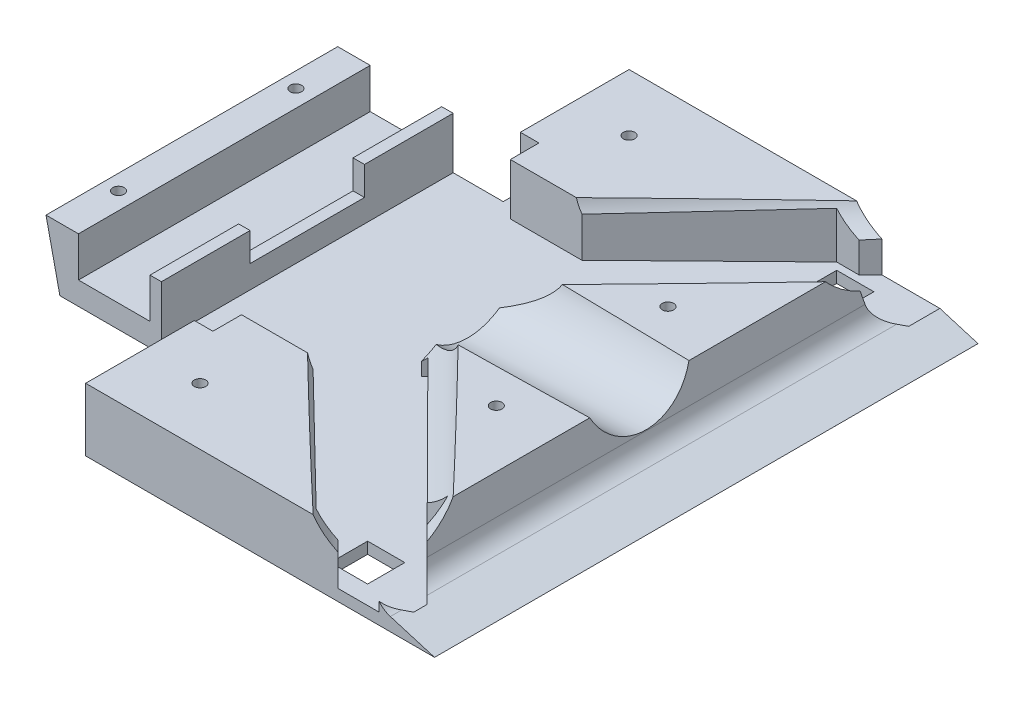
SolidWorks part; units mm, degrees
ref_plane "Front Plane" through (0, 0, 0) normal (0, 0, 1) x (1, 0, 0)
ref_plane "Top Plane" through (0, 0, 0) normal (0, 1, 0) x (1, 0, 0)
ref_plane "Right Plane" through (0, 0, 0) normal (1, 0, 0) x (0, 0, -1)
sketch "Sketch1" plane through (0, 0, 0) normal (0, 1, 0) x (1, 0, 0)
  line L1 (-55.9466, 49.5438) -> (39.0534, 49.5438)
  line L2 (-55.9466, 49.5438) -> (-55.9466, -45.4562)
  line L3 (-55.9466, -45.4562) -> (39.0534, -45.4562)
  line L4 (39.0534, 49.5438) -> (39.0534, -45.4562)
  dimension "D1" = 95
  dimension "D2" = 95
extrude "Boss-Extrude1" add sketch "Sketch1" along normal blind 50
sketch "Sketch2" plane through (0, 0, 45.4562) normal (0, 0, 1) x (1, 0, 0)
  line L0 (39.0534, 0) -> (36.3534, 50)
  line L1 (-55.9466, 50) -> (39.0534, 50) construction
  line L2 (36.3534, 50) -> (39.0534, 50)
  line L3 (39.0534, 50) -> (39.0534, 0)
  dimension "D1" = 2.7
extrude "Cut-Extrude1" cut sketch "Sketch2" against normal blind 100
sketch "Sketch3" plane through (38.9399, 2.1028, 0) normal (0.9985, 0.0539, 0) x (0, 0, -1)
  line L0 (-45.4562, 47.967) -> (-45.4562, -2.1058) construction
  line L1 (-45.4562, -2.1058) -> (49.5438, -2.1058) construction
  circle A0 centre (2.0438, 13.3942) radius 9.5
  point P4 (2.0438, -2.1058)
  dimension "D3" = 19
  dimension "D1" = 47.5
  dimension "D2" = 15.5
extrude "Cut-Extrude2" cut sketch "Sketch3" against normal blind 45
sketch "Sketch5" plane through (0, 50, 0) normal (0, 1, 0) x (1, 0, 0)
  line L0 (39.0534, 49.5438) -> (39.0534, 29.5438)
  line L1 (39.0534, -45.4562) -> (39.0534, 49.5438) construction
  line L2 (39.0534, 29.5438) -> (19.0534, 49.5438)
  line L3 (19.0534, 49.5438) -> (39.0534, 49.5438)
  line L4 (39.0534, -45.4562) -> (39.0534, -25.4562)
  line L5 (39.0534, -25.4562) -> (19.0534, -45.4562)
  line L6 (-55.9466, -45.4562) -> (36.3534, -45.4562) construction
  line L7 (19.0534, -45.4562) -> (39.0534, -45.4562)
  dimension "D1" = 20
  dimension "D2" = 20
  dimension "D3" = 20
  dimension "D4" = 20
extrude "Cut-Extrude4" cut sketch "Sketch5" against normal blind 45
sketch "Sketch6" plane through (0, 50, 0) normal (0, 1, 0) x (1, 0, 0)
  line L0 (19.0534, -45.4562) -> (12.9256, -39.3283)
  line L1 (12.9256, -39.3283) -> (6.7977, -45.4562)
  line L2 (-55.9466, -45.4562) -> (19.0534, -45.4562) construction
  line L3 (6.7977, -45.4562) -> (19.0534, -45.4562)
  line L4 (19.0534, 49.5438) -> (12.9256, 43.4159)
  line L5 (12.9256, 43.4159) -> (6.7977, 49.5438)
  line L6 (19.0534, 49.5438) -> (-55.9466, 49.5438) construction
  line L7 (6.7977, 49.5438) -> (19.0534, 49.5438)
extrude "Cut-Extrude5" cut sketch "Sketch6" against normal blind 45
sketch "Sketch7" plane through (-13.2014, 0, 13.2014) normal (-0.7071, 0, 0.7071) x (0.7071, 0, 0.7071)
  line L0 (45.6152, 5) -> (42.9152, 50)
  line L1 (45.6152, 50) -> (36.9491, 50) construction
  line L2 (42.9152, 50) -> (45.6152, 50)
  line L3 (45.6152, 50) -> (45.6152, 5)
  dimension "D1" = 2.7
extrude "Cut-Extrude6" cut sketch "Sketch7" against normal blind 45
sketch "Sketch8" plane through (-15.2452, 0, -15.2452) normal (-0.7071, 0, -0.7071) x (-0.7071, 0, 0.7071)
  line L0 (-48.5056, 5) -> (-45.8056, 50)
  line L1 (-39.8395, 50) -> (-48.5056, 50) construction
  line L2 (-45.8056, 50) -> (-48.5056, 50)
  line L3 (-48.5056, 50) -> (-48.5056, 5)
  dimension "D1" = 2.7
extrude "Cut-Extrude7" cut sketch "Sketch8" against normal blind 45
sketch "Sketch9" plane through (34.387, 2.9178, -34.387) normal (0.7058, 0.0599, -0.7058) x (-0.7084, 0.0597, -0.7033)
  line L1 (-6.2064, 2.4614) -> (-2.7761, 47.4176) construction
  line L2 (7.1802, -4.1889) -> (74.4757, -4.1889) construction
  circle A0 centre (14.527, 11.3111) radius 9.5
  dimension "D1" = 15.5
  dimension "D2" = 20
extrude "Cut-Extrude9" cut sketch "Sketch9" against normal blind 45
sketch "Sketch11" plane through (32.3505, 2.745, 32.3505) normal (0.7058, 0.0599, 0.7058) x (0.7033, 0.0597, -0.7084)
  line L0 (11.3114, 46.7473) -> (9.3514, 1.703) construction
  line L1 (-71.5478, 4.7302) -> (-4.7333, -3.3019) construction
  circle A0 centre (-10.1775, 12.9642) radius 9.5
  dimension "D1" = 20
  dimension "D2" = 15.5
extrude "Cut-Extrude10" cut sketch "Sketch11" against normal blind 45
sketch "Sketch12" plane through (0, 5, 0) normal (0, 1, 0) x (1, 0, 0)
  line L1 (38.7834, -45.4562) -> (6.7977, -45.4562)
  line L2 (38.7834, -45.4562) -> (38.7834, 49.5438)
  line L3 (38.7834, 49.5438) -> (6.7977, 49.5438)
  line L4 (6.7977, -45.4562) -> (6.7977, 49.5438)
extrude "Boss-Extrude2" add sketch "Sketch12" along normal blind 45
sketch "Sketch13" plane through (0, 0, 45.4562) normal (0, 0, 1) x (1, 0, 0)
  line L0 (39.0534, 0) -> (29.0534, 3)
  line L1 (29.0534, 3) -> (19.0534, 50)
  line L2 (-55.9466, 50) -> (38.7834, 50) construction
  line L3 (19.0534, 50) -> (49.7453, 50)
  line L4 (49.7453, 50) -> (39.0534, 0)
  line L5 (-55.9466, 0) -> (39.0534, 0) construction
  dimension "D1" = 10
  dimension "D2" = 3
  dimension "D3" = 10
extrude "Cut-Extrude11" cut sketch "Sketch13" against normal blind 100
sketch "Sketch14" plane through (-5.9946, -0.3237, 0) normal (0.9985, 0.0539, 0) x (0, 0, -1)
  circle A0 centre (2.0438, 13.3942) radius 9.5
extrude "Cut-Extrude12" cut sketch "Sketch14" along normal blind 100
sketch "Sketch15" plane through (0.5878, 0.0499, 0.5878) normal (0.7058, 0.0599, 0.7058) x (0.7033, 0.0597, -0.7084)
  circle A0 centre (-10.1775, 12.9642) radius 9.5
extrude "Cut-Extrude13" cut sketch "Sketch15" along normal blind 100
sketch "Sketch16" plane through (2.6243, 0.2227, -2.6243) normal (0.7058, 0.0599, -0.7058) x (-0.7084, 0.0597, -0.7033)
  circle A0 centre (14.527, 11.3111) radius 9.5
extrude "Cut-Extrude14" cut sketch "Sketch16" along normal blind 100
fillet "Fillet2" radius 4 1 edges at (29.0534, 3, -2.0438)
sketch "Sketch17" plane through (0, 0, 45.4562) normal (0, 0, 1) x (1, 0, 0)
  line L3 (-55.9466, 0) -> (-21.9466, 0)
  line L4 (-55.9466, 0) -> (-55.9466, 34)
  line L5 (-55.9466, 34) -> (-21.9466, 34)
  line L6 (-21.9466, 0) -> (-21.9466, 34)
  dimension "D1" = 34
  dimension "D2" = 34
extrude "Cut-Extrude16" cut sketch "Sketch17" against normal blind 22
sketch "Sketch19" plane through (0, 0, -49.5438) normal (0, 0, -1) x (-1, 0, 0)
  line L1 (55.9466, 0) -> (21.9466, 0)
  line L2 (55.9466, 0) -> (55.9466, 34)
  line L3 (55.9466, 34) -> (21.9466, 34)
  line L4 (21.9466, 0) -> (21.9466, 34)
  dimension "D1" = 34
  dimension "D2" = 34
extrude "Cut-Extrude17" cut sketch "Sketch19" against normal blind 22
sketch "Sketch20" plane through (0, 0, 23.4562) normal (0, 0, 1) x (1, 0, 0)
  line L0 (-55.9466, 0) -> (-21.9466, 0) construction
  line L1 (-45.1966, 20.5) -> (-32.6966, 20.5)
  line L2 (-45.1966, 20.5) -> (-45.1966, 4)
  line L3 (-45.1966, 4) -> (-32.6966, 4)
  line L4 (-32.6966, 20.5) -> (-32.6966, 4)
  line L5 (-55.9466, 34) -> (-55.9466, 0) construction
  line L6 (-21.9466, 0) -> (-21.9466, 34) construction
  dimension "D1" = 12.5
  dimension "D2" = 16.5
  dimension "D3" = 4
  dimension "D4" = 10.75
  dimension "D5" = 10.75
extrude "Cut-Extrude18" cut sketch "Sketch20" against normal blind 60
sketch "Sketch21" plane through (0, 0, 23.4562) normal (0, 0, 1) x (1, 0, 0)
  line L0 (-55.9466, 34) -> (-48.4466, 0)
  line L1 (-55.9466, 0) -> (-21.9466, 0) construction
  line L2 (-48.4466, 0) -> (-55.9466, 0)
  line L3 (-55.9466, 0) -> (-55.9466, 34)
  dimension "D1" = 7.5
extrude "Cut-Extrude19" cut sketch "Sketch21" against normal blind 60
sketch "Sketch22" plane through (0, 0, 45.4562) normal (0, 0, 1) x (1, 0, 0)
  line L0 (16.5817, 14.4177) -> (-57.7624, 14.4177)
  line L1 (-57.7624, 14.4177) -> (-57.7624, 55.8779)
  line L2 (-57.7624, 55.8779) -> (42.054, 55.8779)
  line L3 (42.054, 55.8779) -> (42.054, 14.4177)
  line L4 (42.054, 14.4177) -> (16.5817, 14.4177)
  ellipse E0 centre (29.9926, 15.5557) end of major axis (16.5817, 14.4177) minor radius 9.5 (24.5777, 24.0358) -> (28.4071, 6.0379) ccw construction
extrude "Cut-Extrude20" cut sketch "Sketch22" against normal blind 100
sketch "Sketch23" plane through (0, 0, 45.4562) normal (0, 0, 1) x (1, 0, 0)
  line L1 (-51.6269, 14.4177) -> (45.1591, 14.4177)
  line L2 (-51.6269, 14.4177) -> (-51.6269, 11.4177)
  line L3 (-51.6269, 11.4177) -> (45.1591, 11.4177)
  line L4 (45.1591, 14.4177) -> (45.1591, 11.4177)
  dimension "D1" = 3
extrude "Cut-Extrude21" cut sketch "Sketch23" against normal blind 1090
sketch "Sketch25" plane through (0, 11.4177, 0) normal (0, 1, 0) x (1, 0, 0)
  line L1 (-14.3105, -14.5215) -> (-2.7353, -14.5215)
  line L2 (-14.3105, -14.5215) -> (-14.3105, 7.5358)
  line L4 (-2.7353, -14.5215) -> (-2.7353, 7.5358)
  line L5 (-14.3105, 18.6091) -> (-2.7353, 18.6091)
  line L6 (-14.3105, 18.6091) -> (-14.3105, 7.5358)
  line L8 (-2.7353, 18.6091) -> (-2.7353, 7.5358)
extrude "Cut-Extrude23" cut sketch "Sketch25" against normal blind 9
sketch "Sketch26" plane through (0, 0, 45.4562) normal (0, 0, 1) x (1, 0, 0)
  line L1 (46.1318, 11) -> (-55.111, 11)
  line L2 (46.1318, 11) -> (46.1318, 34.1811)
  line L3 (46.1318, 34.1811) -> (-55.111, 34.1811)
  line L4 (-55.111, 11) -> (-55.111, 34.1811)
  dimension "D1" = 11
extrude "Cut-Extrude24" cut sketch "Sketch26" against normal blind 1212
sketch "Sketch27" plane through (0, 11, 0) normal (0, 1, 0) x (1, 0, 0)
  line L0 (17.8279, -45.4562) -> (28.4071, -45.4562) construction
  line L1 (25.3513, -29.4562) -> (16.3513, -29.4562)
  line L2 (25.3513, -29.4562) -> (25.3513, -43.4562)
  line L3 (25.3513, -43.4562) -> (16.3513, -43.4562)
  line L4 (16.3513, -29.4562) -> (16.3513, -43.4562)
  line L5 (-21.9466, 49.5438) -> (17.8279, 49.5438) construction
  line L6 (25.3513, 33.5438) -> (16.3513, 33.5438)
  line L7 (25.3513, 33.5438) -> (25.3513, 47.5438)
  line L8 (25.3513, 47.5438) -> (16.3513, 47.5438)
  line L9 (16.3513, 33.5438) -> (16.3513, 47.5438)
  dimension "D1" = 9
  dimension "D2" = 14
  dimension "D3" = 2
  dimension "D4" = 2
  dimension "D5" = 14
  dimension "D6" = 2
extrude "Cut-Extrude25" cut sketch "Sketch27" against normal blind 9
sketch "Sketch32" plane through (0, 11, 0) normal (0, 1, 0) x (1, 0, 0)
  line L0 (16.3513, -43.4562) -> (-14.3105, -13.5215)
  line L1 (-14.3105, 18.6091) -> (-14.3105, -14.5215) construction
  line L2 (16.3513, -43.4562) -> (16.3513, -38.4562)
  line L3 (16.3513, -29.4562) -> (16.3513, -43.4562) construction
  line L4 (16.3513, -38.4562) -> (-14.3105, -8.5215)
  line L5 (-14.3105, -8.5215) -> (-14.3105, -13.5215)
  line L6 (16.3513, 47.5438) -> (-14.3105, 17.6091)
  line L7 (-14.3105, 18.6091) -> (-14.3105, -14.5215) construction
  line L8 (-14.3105, 17.6091) -> (-14.3105, 12.6091)
  line L9 (-14.3105, 12.6091) -> (16.3513, 42.5438)
  line L10 (16.3513, 47.5438) -> (16.3513, 33.5438) construction
  line L11 (16.3513, 42.5438) -> (16.3513, 47.5438)
  dimension "D1" = 1
  dimension "D2" = 5
  dimension "D3" = 5
  dimension "D4" = 5
  dimension "D5" = 5
  dimension "D6" = 1
extrude "Cut-Extrude30" cut sketch "Sketch32" against normal blind 9
sketch "Sketch33" plane through (0, 2, 0) normal (0, 1, 0) x (1, 0, 0)
  line L0 (16.3513, -43.4562) -> (25.3513, -43.4562) construction
  line L1 (18.3513, -36.4562) -> (23.3513, -36.4562)
  line L2 (18.3513, -36.4562) -> (18.3513, -41.4562)
  line L3 (18.3513, -41.4562) -> (23.3513, -41.4562)
  line L4 (23.3513, -36.4562) -> (23.3513, -41.4562)
  line L5 (25.3513, -43.4562) -> (25.3513, -29.4562) construction
  line L7 (18.3513, 45.5438) -> (23.3513, 45.5438)
  line L8 (18.3513, 45.5438) -> (18.3513, 40.5438)
  line L9 (18.3513, 40.5438) -> (23.3513, 40.5438)
  line L10 (23.3513, 45.5438) -> (23.3513, 40.5438)
  line L12 (16.3513, 47.5438) -> (25.3513, 47.5438) construction
  dimension "D1" = 2
  dimension "D2" = 2
  dimension "D3" = 5
  dimension "D4" = 5
  dimension "D5" = 5
  dimension "D6" = 2
extrude "Cut-Extrude31" cut sketch "Sketch33" against normal blind 9
sketch "Sketch34" plane through (0, 11, 0) normal (0, 1, 0) x (1, 0, 0)
  line L1 (-14.3105, 18.6091) -> (-2.7353, 18.6091)
  line L2 (-14.3105, 18.6091) -> (-14.3105, -14.5215)
  line L3 (-14.3105, -14.5215) -> (-2.7353, -14.5215)
  line L4 (-2.7353, 18.6091) -> (-2.7353, -14.5215)
extrude "Cut-Extrude32" cut sketch "Sketch34" against normal blind 9
sketch "Sketch35" plane through (0, 11, 0) normal (0, 1, 0) x (1, 0, 0)
  line L0 (-21.9466, 27.5438) -> (-32.6966, 27.5438) construction
  line L1 (-15.6966, 25.5438) -> (-30.6966, 25.5438)
  line L2 (-15.6966, 25.5438) -> (-15.6966, -21.4562)
  line L3 (-15.6966, -21.4562) -> (-30.6966, -21.4562)
  line L4 (-30.6966, 25.5438) -> (-30.6966, -21.4562)
  line L5 (-32.6966, -23.4562) -> (-32.6966, 27.5438) construction
  line L6 (-21.9466, -23.4562) -> (-32.6966, -23.4562) construction
  line L7 (-14.3105, 18.6091) -> (-14.3105, -14.5215) construction
  dimension "D1" = 2
  dimension "D2" = 2
  dimension "D3" = 2
  dimension "D4" = 15
  dimension "D5" = 1.386
extrude "Cut-Extrude33" cut sketch "Sketch35" against normal blind 9
sketch "Sketch36" plane through (0, 11, 0) normal (0, 1, 0) x (1, 0, 0)
  line L0 (-15.6966, -21.4562) -> (-15.6966, 25.5438) construction
  line L1 (-14.3105, -14.5215) -> (-15.6966, -14.5215)
  line L2 (-14.3105, -14.5215) -> (-14.3105, 18.6091)
  line L3 (-14.3105, 18.6091) -> (-15.6966, 18.6091)
  line L4 (-15.6966, -14.5215) -> (-15.6966, 18.6091)
  dimension "D1" = 0
extrude "Cut-Extrude34" cut sketch "Sketch36" against normal blind 9
sketch "Sketch37" plane through (0, 11, 0) normal (0, 1, 0) x (1, 0, 0)
  line L0 (-30.6966, 25.5438) -> (-30.6966, -21.4562) construction
  line L1 (-30.6966, 12.0438) -> (-32.6966, 12.0438)
  line L2 (-30.6966, 12.0438) -> (-30.6966, -7.9562)
  line L3 (-30.6966, -7.9562) -> (-32.6966, -7.9562)
  line L4 (-32.6966, 12.0438) -> (-32.6966, -7.9562)
  line L5 (-32.6966, -23.4562) -> (-32.6966, 27.5438) construction
  dimension "D1" = 20
  dimension "D2" = 15.5
  dimension "D3" = 15.5
extrude "Cut-Extrude35" cut sketch "Sketch37" against normal blind 5
sketch "Sketch38" plane through (0, 11, 0) normal (0, 1, 0) x (1, 0, 0)
  line L0 (-21.9466, 27.5438) -> (-21.9466, 49.5438) construction
  line L1 (-21.9466, 49.5438) -> (17.8279, 49.5438) construction
  line L3 (-21.9466, -45.4562) -> (17.8279, -45.4562) construction
  line L4 (27.3513, 34.5905) -> (27.3513, 10.7131) construction
  line L5 (28.5603, -45.4562) -> (28.5603, 49.5438) construction
  circle A0 centre (-11.9466, 39.5438) radius 1
  circle A1 centre (-11.9466, -35.4562) radius 1
  circle A2 centre (17.3513, 17.0438) radius 1
  circle A3 centre (17.3513, -12.9562) radius 1
  ellipse E0 centre (26.5329, 2.0438) end of major axis (26.5329, -7.4562) minor radius 2.0012 (27.3513, -6.6255) -> (27.3513, 10.7131) ccw construction
  point P14 (28.5603, 2.0438)
  point P19 (28.5342, 2.0438)
  dimension "D1" = 10
  dimension "D3" = 10
  dimension "D4" = 10
  dimension "D6" = 15
  dimension "D2" = 10
  dimension "D5" = 15
extrude "Cut-Extrude36" cut sketch "Sketch38" against normal blind 5
sketch "Sketch39" plane through (0, 11, 0) normal (0, 1, 0) x (1, 0, 0)
  line L0 (-45.1966, 27.5438) -> (-45.1966, -23.4562) construction
  line L1 (-45.1966, 27.5438) -> (-50.873, 27.5438) construction
  line L2 (-45.1966, -23.4562) -> (-50.873, -23.4562) construction
  circle A0 centre (-48.1966, 17.5438) radius 1
  circle A1 centre (-48.1966, -13.4562) radius 1
  dimension "D1" = 3
  dimension "D3" = 10
  dimension "D2" = 10
extrude "Cut-Extrude37" cut sketch "Sketch39" against normal blind 5
sketch "Sketch40" plane through (0, 11, 0) normal (0, 1, 0) x (1, 0, 0)
  line L2 (-15.6966, 25.5438) -> (-2.6472, 25.5438)
  line L3 (-15.6966, 25.5438) -> (-15.6966, -14.2692)
  line L6 (-2.6472, 25.5438) -> (-2.6472, -14.2692)
  line L7 (-15.6966, -21.4562) -> (-2.6472, -21.4562)
  line L8 (-15.6966, -21.4562) -> (-15.6966, -14.2692)
  line L10 (-2.6472, -21.4562) -> (-2.6472, -14.2692)
extrude "Cut-Extrude39" cut sketch "Sketch40" against normal blind 9
sketch "Sketch41" plane through (0, 11, 0) normal (0, 1, 0) x (1, 0, 0)
  line L0 (16.3513, 47.5438) -> (16.3513, 40.0438)
  line L1 (16.3513, 42.5438) -> (16.3513, 33.5438) construction
  line L2 (16.3513, 40.0438) -> (-2.6472, 21.7292)
  line L3 (-2.6472, -19.9083) -> (-2.6472, 23.9959) construction
  line L4 (-2.6472, 21.7292) -> (-4.186, 23.3255)
  line L5 (-4.186, 23.3255) -> (16.3513, 47.5438)
  dimension "D1" = 7.5
extrude "Cut-Extrude40" cut sketch "Sketch41" against normal blind 9
sketch "Sketch42" plane through (0, 11, 0) normal (0, 1, 0) x (1, 0, 0)
  line L0 (16.3513, -43.4562) -> (16.3513, -35.9562)
  line L1 (16.3513, -38.4562) -> (16.3513, -29.4562) construction
  line L2 (16.3513, -35.9562) -> (-5.3341, -15.1374)
  line L4 (-5.3341, -15.1374) -> (-2.787, -23.0755)
  line L5 (-2.787, -23.0755) -> (16.3513, -43.4562)
  dimension "D1" = 7.5
extrude "Cut-Extrude41" cut sketch "Sketch42" against normal blind 9
sketch "Sketch44" plane through (0, 2, 0) normal (0, 1, 0) x (1, 0, 0)
  line L1 (17.6013, -35.7062) -> (24.1013, -35.7062)
  line L2 (17.6013, -35.7062) -> (17.6013, -42.2062)
  line L3 (17.6013, -42.2062) -> (24.1013, -42.2062)
  line L4 (24.1013, -35.7062) -> (24.1013, -42.2062)
  line L5 (17.6013, 46.2938) -> (24.1013, 46.2938)
  line L6 (17.6013, 46.2938) -> (17.6013, 39.7938)
  line L7 (17.6013, 39.7938) -> (24.1013, 39.7938)
  line L8 (24.1013, 46.2938) -> (24.1013, 39.7938)
  dimension "D1" = 0.75
  dimension "D2" = 0.75
  dimension "D3" = 0.75
  dimension "D4" = 0.75
  dimension "D5" = 0.75
  dimension "D6" = 0.75
  dimension "D7" = 0.75
  dimension "D8" = 0.75
extrude "Cut-Extrude42" cut sketch "Sketch44" against normal blind 9
sketch "Sketch45" plane through (0, 11, 0) normal (0, 1, 0) x (1, 0, 0)
  line L0 (-21.9466, -23.4562) -> (-32.6966, -23.4562) construction
  line L1 (-18.6966, 30.5438) -> (-30.6966, 30.5438)
  line L2 (-18.6966, 30.5438) -> (-18.6966, -26.4562)
  line L3 (-18.6966, -26.4562) -> (-30.6966, -26.4562)
  line L4 (-30.6966, 30.5438) -> (-30.6966, -26.4562)
  line L5 (-21.9466, 27.5438) -> (-32.6966, 27.5438) construction
  dimension "D1" = 57
  dimension "D2" = 12
  dimension "D3" = 3
  dimension "D4" = 3
  dimension "D5" = 0
extrude "Cut-Extrude44" cut sketch "Sketch45" against normal blind 9
sketch "Sketch46" plane through (0, 11, 0) normal (0, 1, 0) x (1, 0, 0)
  line L0 (-9.877, -13.2474) -> (-2.0803, -5.4877)
  line L1 (-2.0803, -5.4877) -> (33.5415, -41.2791)
  line L2 (33.5415, -41.2791) -> (25.7449, -49.0388)
  line L3 (25.7449, -49.0388) -> (-9.877, -13.2474)
  line L4 (-4.3774, 22.9107) -> (34.6557, 61.9438)
  line L5 (34.6557, 61.9438) -> (42.4339, 54.1656)
  line L6 (42.4339, 54.1656) -> (0.7912, 12.523)
  line L8 (-4.3774, 22.9107) -> (-6.987, 20.3011)
  line L9 (0.7912, 12.523) -> (-6.987, 4.7448)
  line L10 (-6.987, 4.7448) -> (-6.987, 20.3011)
  ellipse E0 centre (-23.6968, -4.1456) end of major axis (88.4631, 108.0143) minor radius 9.5 (4.7868, 11.1614) -> (27.3513, 34.5905) ccw construction
  ellipse E1 centre (-23.6968, 8.2332) end of major axis (88.4631, -103.9267) minor radius 9.5 (27.3513, -30.5029) -> (4.7868, -7.0738) ccw construction
  ellipse E2 centre (-23.6968, 8.2332) end of major axis (88.4631, -103.9267) minor radius 9.5 (-7.1539, -21.4562) -> (17.8279, -45.4562) ccw construction
  point P4 (16.1105, -18.7484)
  point P7 (5.2909, -33.5042)
  point P16 (16.1105, 22.836)
  dimension "D1" = 11
  dimension "D2" = 3.54
  dimension "D3" = 3.539
  dimension "D4" = 11
extrude "Cut-Extrude48" cut sketch "Sketch46" against normal up to surface (9 mm away) up to face at (20.8513, 2, -43.0438)
